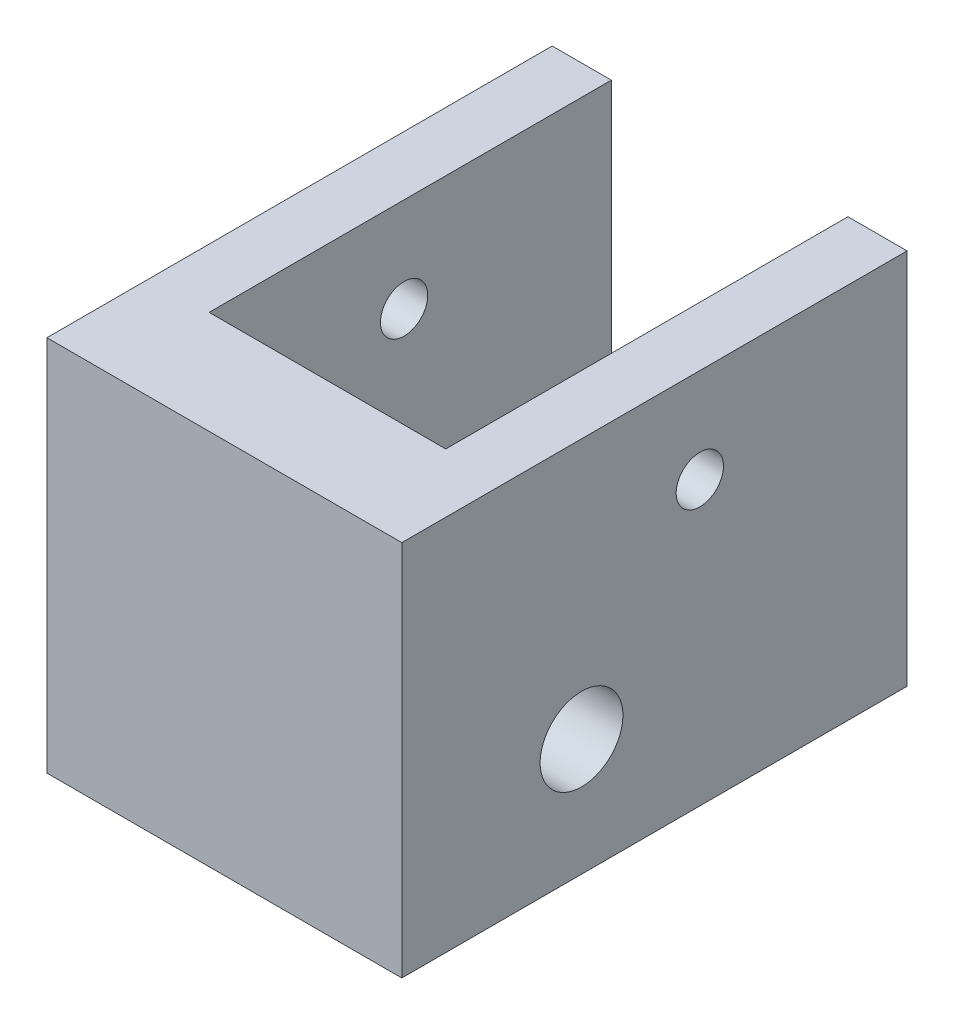
SolidWorks part; units mm, degrees
ref_plane "Front Plane" through (0, 0, 0) normal (0, 0, 1) x (1, 0, 0)
ref_plane "Top Plane" through (0, 0, 0) normal (0, 1, 0) x (1, 0, 0)
ref_plane "Right Plane" through (0, 0, 0) normal (1, 0, 0) x (0, 0, -1)
sketch "Sketch1" plane through (0, 0, 0) normal (1, 0, 0) x (0, 0, -1)
  line L3 (2.8334, 8.5165) -> (7.1666, 5.4835) construction
  line L5 (13.7596, 10.9906) -> (-7.5971, 10.9906)
  line L6 (13.7596, 10.9906) -> (13.7596, -4.9468)
  line L7 (13.7596, -4.9468) -> (-7.5971, -4.9468)
  line L8 (-7.5971, 10.9906) -> (-7.5971, -4.9468)
  circle A0 centre (0, 0) radius 1.75
  circle A1 centre (5, 7) radius 1
  point P9 (13.7596, -4.9468)
  dimension "D1" = 2
  dimension "D2" = 3.5
  dimension "D3" = 6
  dimension "D4" = 7
extrude "Boss-Extrude1" add sketch "Sketch1" along normal blind 15
sketch "Sketch2" plane through (0, 10.9906, 0) normal (0, 1, 0) x (1, 0, 0)
  line L0 (15, 13.7596) -> (0, 13.7596) construction
  line L1 (2.5, 13.7596) -> (12.5, 13.7596)
  line L2 (2.5, 13.7596) -> (2.5, -3.2404)
  line L3 (2.5, -3.2404) -> (12.5, -3.2404)
  line L4 (12.5, 13.7596) -> (12.5, -3.2404)
  line L5 (15, -7.5971) -> (0, -7.5971) construction
  point P8 (7.5, -7.5971)
  point P9 (7.5, -3.2404)
  dimension "D1" = 10
  dimension "D2" = 17
extrude "Cut-Extrude1" cut sketch "Sketch2" against normal up to next
